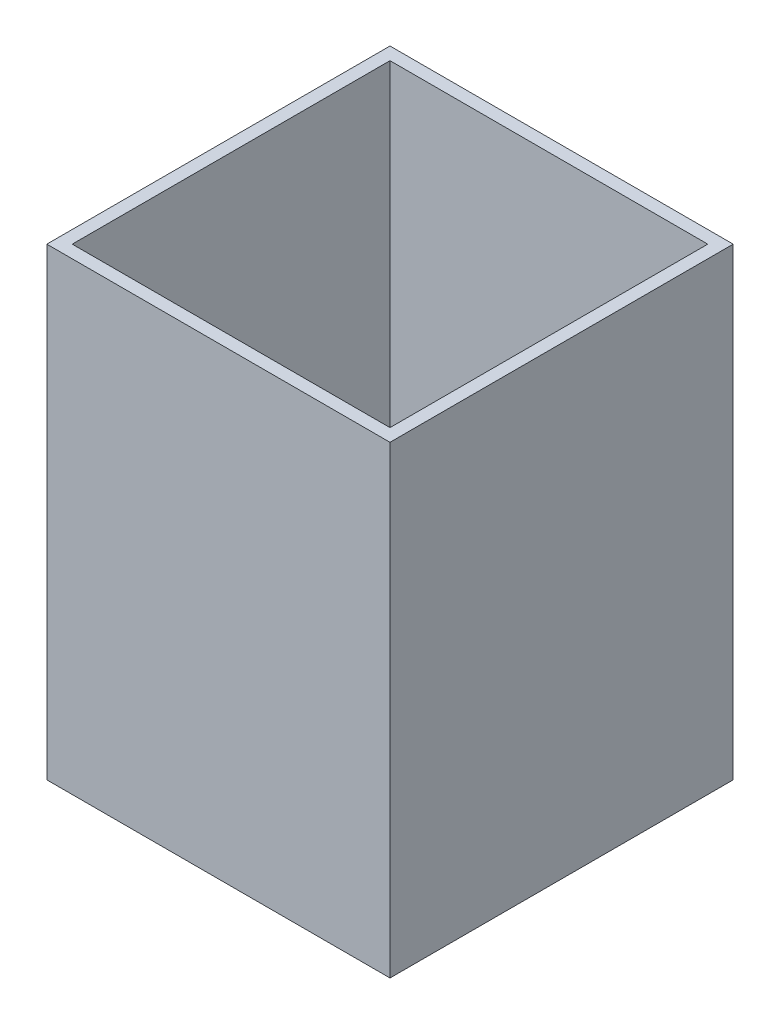
SolidWorks part; units mm, degrees
ref_plane "Front Plane" through (0, 0, 0) normal (0, 0, 1) x (1, 0, 0)
ref_plane "Top Plane" through (0, 0, 0) normal (0, 1, 0) x (1, 0, 0)
ref_plane "Right Plane" through (0, 0, 0) normal (1, 0, 0) x (0, 0, -1)
sketch "Sketch1" plane through (0, 0, 0) normal (0, 1, 0) x (1, 0, 0)
  line L1 (-25, -25) -> (25, -25)
  line L2 (-25, -25) -> (-25, 25)
  line L3 (-25, 25) -> (25, 25)
  line L4 (25, -25) -> (25, 25)
  line L5 (-25, -25) -> (25, 25) construction
  line L6 (-25, 25) -> (25, -25) construction
  line L7 (-27, -27) -> (27, -27)
  line L8 (-27, -27) -> (-27, 27)
  line L9 (-27, 27) -> (27, 27)
  line L10 (27, -27) -> (27, 27)
  line L11 (-27, -27) -> (27, 27) construction
  line L12 (-27, 27) -> (27, -27) construction
  point P0 (0, 0)
  point P6 (0, 0)
  dimension "D1" = 50
  dimension "D2" = 50
  dimension "D3" = 2
  dimension "D4" = 2
extrude "Boss-Extrude1" add sketch "Sketch1" along normal blind 22
sketch "Sketch2" plane through (0, 22, 0) normal (0, 1, 0) x (1, 0, 0)
  line L1 (-27, -27) -> (27, -27)
  line L2 (-27, -27) -> (-27, 27)
  line L3 (-27, 27) -> (27, 27)
  line L4 (27, -27) -> (27, 27)
  line L5 (-27, -27) -> (27, 27) construction
  line L6 (-27, 27) -> (27, -27) construction
  point P0 (0, 0)
extrude "Boss-Extrude2" add sketch "Sketch2" along normal blind 1
sketch "Sketch3" plane through (0, 23, 0) normal (0, 1, 0) x (1, 0, 0)
  circle A0 centre (0, 0) radius 6
  dimension "D1" = 12
extrude "Cut-Extrude1" cut sketch "Sketch3" against normal through all
sketch "Sketch4" plane through (0, 23, 0) normal (0, 1, 0) x (1, 0, 0)
  line L0 (27, -27) -> (27, 27) construction
  line L1 (-27, 27) -> (27, 27)
  line L2 (-27, 27) -> (-27, 25)
  line L3 (-27, 25) -> (27, 25)
  line L4 (27, 27) -> (27, 25)
  line L5 (-27, -27) -> (27, -27) construction
  line L6 (27, 27) -> (25, 27)
  line L7 (27, 27) -> (27, -27)
  line L8 (27, -27) -> (25, -27)
  line L9 (25, 27) -> (25, -27)
  line L11 (-27, -27) -> (27, -27)
  line L12 (-27, -27) -> (-27, -25)
  line L13 (-27, -25) -> (27, -25)
  line L14 (27, -27) -> (27, -25)
  line L15 (-27, 27) -> (-25, 27)
  line L16 (-27, 27) -> (-27, -27)
  line L17 (-27, -27) -> (-25, -27)
  line L18 (-25, 27) -> (-25, -27)
  line M10 (27, -27) -> (27, 27)
  line M11 (27, 27) -> (-27, 27)
  line M12 (-27, 27) -> (-27, -27)
  line M13 (-27, -27) -> (27, -27)
  dimension "D1" = 2
  dimension "D2" = 2
  dimension "D3" = 2
  dimension "D4" = 2
extrude "Boss-Extrude3" add sketch "Sketch4" along normal blind 50 contours L18 L3 L13 M12 | L18 L13 M12 M13 | L13 L18 L11 L9 | L13 L9 M13 M10 | L9 L13 L7 L3 | L9 L3 M11 M10 | L1 L18 L3 L9 | L18 L3 M11 M12
